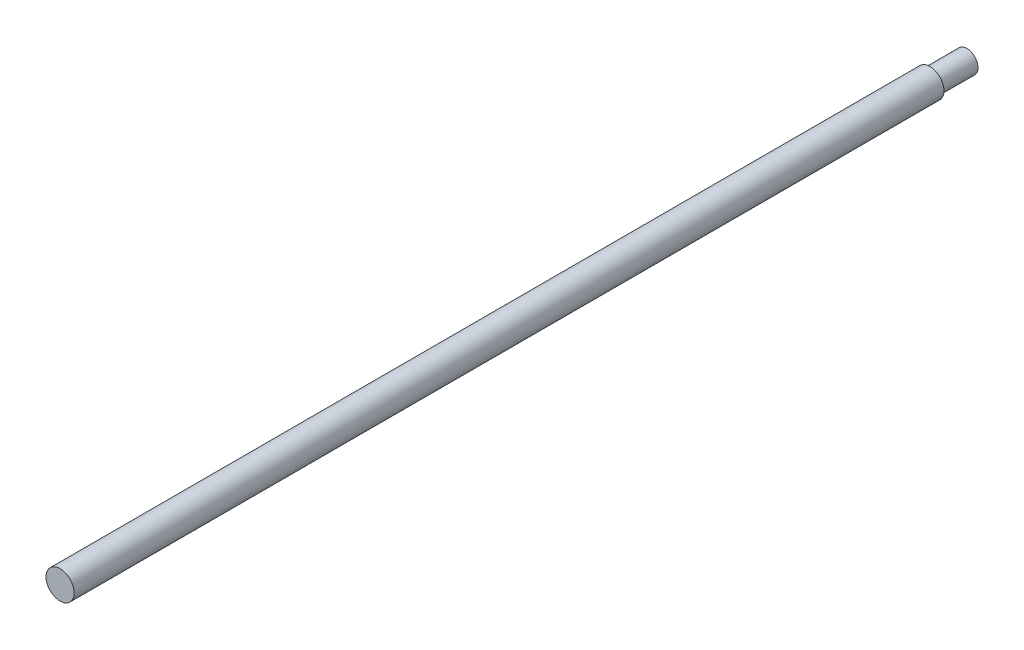
SolidWorks part; units mm, degrees
ref_plane "Front Plane" through (0, 0, 0) normal (0, 0, 1) x (1, 0, 0)
ref_plane "Top Plane" through (0, 0, 0) normal (0, 1, 0) x (1, 0, 0)
ref_plane "Right Plane" through (0, 0, 0) normal (1, 0, 0) x (0, 0, -1)
sketch "Sketch1" plane through (0, 0, 0) normal (0, 0, 1) x (1, 0, 0)
  circle A0 centre (0, 0) radius 3.8
  dimension "D1" = 7.6
extrude "Boss-Extrude1" add sketch "Sketch1" along normal blind 245
sketch "Sketch2" plane through (0, 0, 0) normal (0, 0, -1) x (-1, 0, 0)
  circle A0 centre (0, 0) radius 3
  dimension "D1" = 6
extrude "Cut-Extrude1" cut sketch "Sketch2" against normal blind 10 flip side to cut
